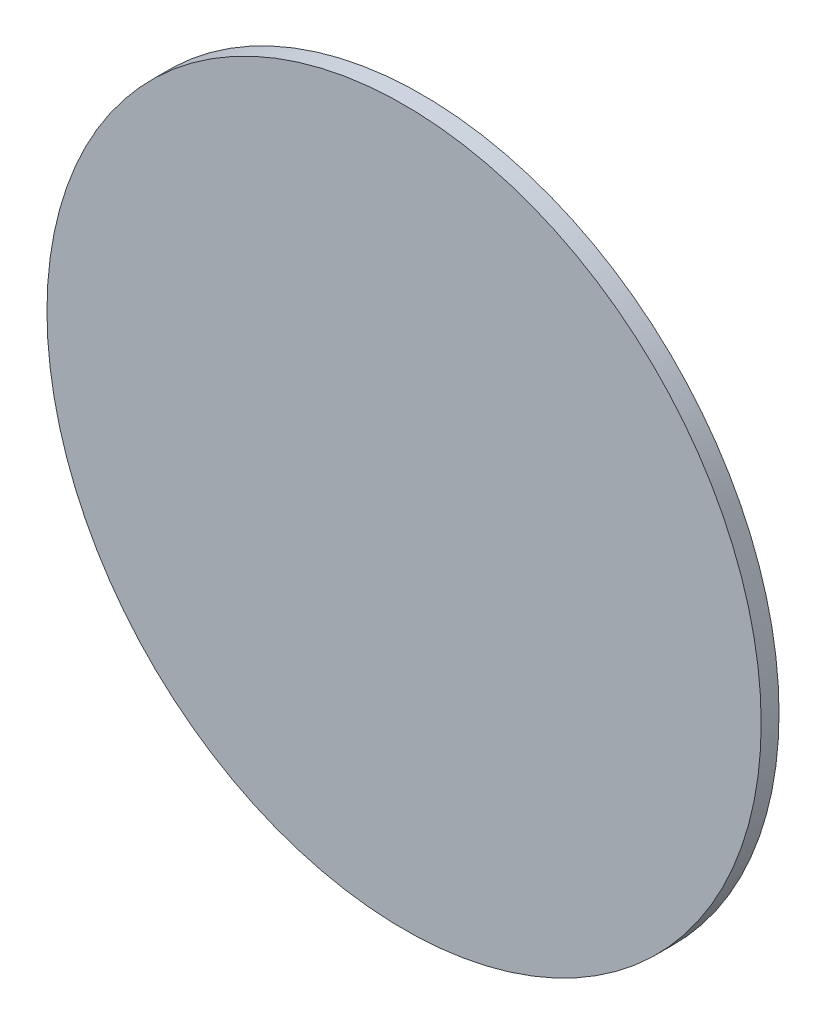
SolidWorks part; units mm, degrees
ref_plane "Front Plane" through (0, 0, 0) normal (0, 0, 1) x (1, 0, 0)
ref_plane "Top Plane" through (0, 0, 0) normal (0, 1, 0) x (1, 0, 0)
ref_plane "Right Plane" through (0, 0, 0) normal (1, 0, 0) x (0, 0, -1)
sketch "Sketch1" plane through (0, 0, 0) normal (0, 0, 1) x (1, 0, 0)
  circle A0 centre (0, 0) radius 63.5
  dimension "D1" = 127
extrude "Boss-Extrude1" add sketch "Sketch1" along normal blind 3.175
